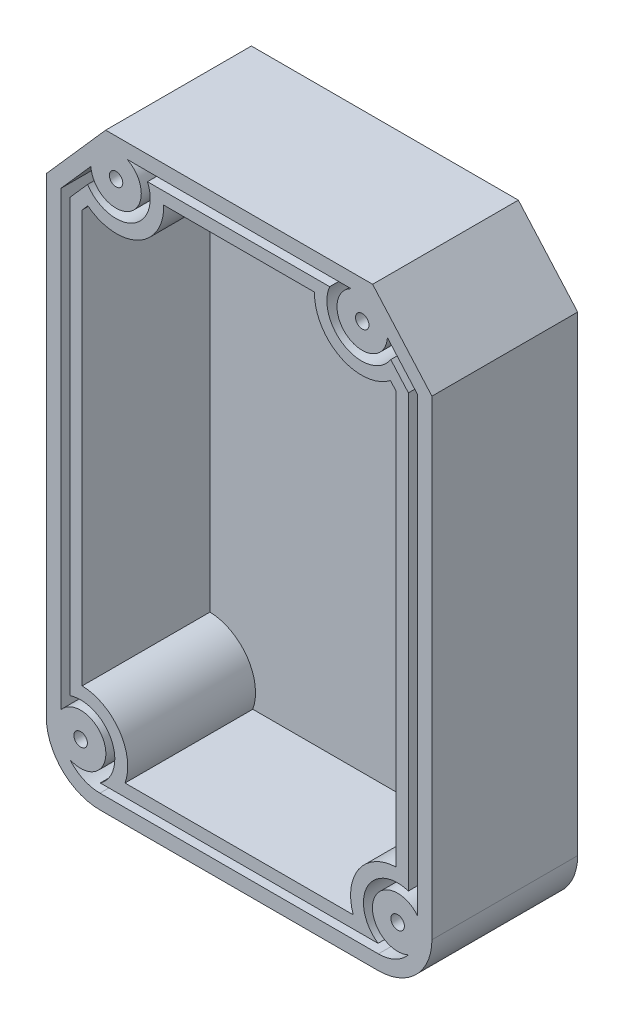
SolidWorks part; units mm, degrees
ref_plane "Front Plane" through (0, 0, 0) normal (0, 0, 1) x (1, 0, 0)
ref_plane "Top Plane" through (0, 0, 0) normal (0, 1, 0) x (1, 0, 0)
ref_plane "Right Plane" through (0, 0, 0) normal (1, 0, 0) x (0, 0, -1)
sketch "Sketch1" plane through (0, 0, 0) normal (0, 0, 1) x (1, 0, 0)
  line L3 (-1355.6942, -734.7459) -> (-1355.6942, -839.7459)
  line L4 (-1367.6432, -851.6949) -> (-1429.7452, -851.6949)
  line L5 (-1441.6942, -839.7459) -> (-1441.6942, -734.7459)
  line L6 (-1441.6942, -734.7459) -> (-1428.4655, -719.7459)
  line L7 (-1428.4655, -719.7459) -> (-1368.923, -719.7459)
  line L8 (-1368.923, -719.7459) -> (-1355.6942, -734.7459)
  arc A0 (-1355.6942, -839.7459) -> (-1367.6432, -851.6949) centre (-1367.6432, -839.7459) cw
  arc A1 (-1429.7452, -851.6949) -> (-1441.6942, -839.7459) centre (-1429.7452, -839.7459) cw
  dimension "D5" = 11.949
  dimension "D6" = 11.949
  dimension "D1" = 105
  dimension "D2" = 86
  dimension "D3" = 15
  dimension "D4" = 20
extrude "Boss-Extrude1" add sketch "Sketch1" along normal blind 32.5 contours L3 A0 L4 A1 L5 L6 L7 L8
sketch "Sketch2" plane through (0, 0, 32.5) normal (0, 0, 1) x (1, 0, 0)
  line L6 (-1355.6942, -734.7459) -> (-1368.923, -719.7459)
  line L7 (-1368.923, -719.7459) -> (-1428.4655, -719.7459)
  line L8 (-1428.4655, -719.7459) -> (-1441.6942, -734.7459)
  line L9 (-1441.6942, -734.7459) -> (-1441.6942, -839.7459)
  line L10 (-1429.7452, -851.6949) -> (-1367.6432, -851.6949)
  line L11 (-1355.6942, -839.7459) -> (-1355.6942, -734.7459)
  line L12 (-1355.6942, -734.7459) -> (-1368.923, -719.7459)
  line L13 (-1368.923, -719.7459) -> (-1428.4655, -719.7459)
  line L14 (-1428.4655, -719.7459) -> (-1441.6942, -734.7459)
  line L15 (-1441.6942, -734.7459) -> (-1441.6942, -839.7459)
  line L16 (-1429.7452, -851.6949) -> (-1367.6432, -851.6949)
  line L17 (-1355.6942, -839.7459) -> (-1355.6942, -734.7459)
  line L18 (-1358.9442, -735.9743) -> (-1370.3901, -722.9959)
  line L19 (-1370.3901, -722.9959) -> (-1426.9984, -722.9959)
  line L20 (-1426.9984, -722.9959) -> (-1438.4442, -735.9743)
  line L21 (-1438.4442, -735.9743) -> (-1438.4442, -839.7459)
  line L22 (-1429.7452, -848.4449) -> (-1367.6432, -848.4449)
  line L23 (-1358.9442, -839.7459) -> (-1358.9442, -735.9743)
  arc A2 (-1441.6942, -839.7459) -> (-1429.7452, -851.6949) centre (-1429.7452, -839.7459) ccw
  arc A3 (-1367.6432, -851.6949) -> (-1355.6942, -839.7459) centre (-1367.6432, -839.7459) ccw
  arc A4 (-1441.6942, -839.7459) -> (-1429.7452, -851.6949) centre (-1429.7452, -839.7459) ccw
  arc A5 (-1367.6432, -851.6949) -> (-1355.6942, -839.7459) centre (-1367.6432, -839.7459) ccw
  arc A6 (-1438.4442, -839.7459) -> (-1429.7452, -848.4449) centre (-1429.7452, -839.7459) ccw
  arc A7 (-1367.6432, -848.4449) -> (-1358.9442, -839.7459) centre (-1367.6432, -839.7459) ccw
  dimension "D1" = 0
  dimension "D2" = 3.25
extrude "Cut-Extrude3" cut sketch "Sketch2" along direction (0, 0, -1) on the side against the normal offset from surface 4 and the other way through all contours L18 L19 L20 L21 A6 L22 A7 L23
sketch "Sketch32" plane through (0, 0, 4) normal (0, 0, 1) x (1, 0, 0)
  line L2 (-1398.6942, -848.4449) -> (-1398.6942, -844.105) construction
  line L3 (-1429.7452, -848.4449) -> (-1367.6432, -848.4449) construction
  line L10 (-1358.9442, -839.7459) -> (-1358.9442, -735.9743)
  line L11 (-1358.9442, -735.9743) -> (-1370.3901, -722.9959)
  line L12 (-1370.3901, -722.9959) -> (-1426.9984, -722.9959)
  line L13 (-1426.9984, -722.9959) -> (-1438.4442, -735.9743)
  line L14 (-1438.4442, -735.9743) -> (-1438.4442, -839.7459)
  line L15 (-1429.7452, -848.4449) -> (-1367.6432, -848.4449)
  line L21 (-1398.6942, -848.4449) -> (-1367.6432, -848.4449)
  circle A8 centre (-1426.1484, -728.0459) radius 1.5
  circle A9 centre (-1426.1484, -728.0459) radius 5.625
  arc A10 (-1438.4442, -839.7459) -> (-1429.7452, -848.4449) centre (-1429.7452, -839.7459) ccw
  arc A11 (-1367.6432, -848.4449) -> (-1358.9442, -839.7459) centre (-1367.6432, -839.7459) ccw
  circle A14 centre (-1371.2401, -728.0459) radius 1.5
  circle A15 centre (-1371.2401, -728.0459) radius 5.625
  circle A16 centre (-1434.0452, -840.1949) radius 1.5
  circle A17 centre (-1434.0452, -840.1949) radius 5.625
  circle A18 centre (-1363.3432, -840.1949) radius 1.5
  circle A19 centre (-1363.3432, -840.1949) radius 5.625
  dimension "D2" = 3
  dimension "D5" = 0.85
  dimension "D6" = 0.85
  dimension "D9" = 4.3
  dimension "D10" = 11.25
  dimension "D3" = 11.25
  dimension "D4" = 5.05
  dimension "D7" = 8.25
  dimension "D8" = 4.3
  dimension "D11" = 0
extrude "Boss-Extrude5" add sketch "Sketch32" along direction (0, 0, -1) on the side of the normal up to surface (28.5 mm away) contours A9 | A15 | A17 | A19 | A8 | A14 | A18 | A16
sketch "Sketch33" plane through (0, 0, 4) normal (0, 0, 1) x (1, 0, 0)
  circle A8 centre (-1363.3432, -840.1949) radius 1.5 construction
  circle A9 centre (-1434.0452, -840.1949) radius 1.5 construction
  circle A10 centre (-1426.1484, -728.0459) radius 1.5 construction
  circle A11 centre (-1371.2401, -728.0459) radius 1.5 construction
  circle A12 centre (-1363.3432, -840.1949) radius 1.5
  circle A13 centre (-1434.0452, -840.1949) radius 1.5
  circle A14 centre (-1426.1484, -728.0459) radius 1.5
  circle A15 centre (-1371.2401, -728.0459) radius 1.5
  dimension "D1" = 3
extrude "Cut-Extrude15" cut sketch "Sketch33" along direction (0, 0, -1) on the side against the normal up to surface (4 mm away)
sketch "Sketch34" plane through (0, 0, 4) normal (0, 0, 1) x (1, 0, 0)
  line L31 (-1429.4626, -846.4449) -> (-1367.9258, -846.4449)
  line L32 (-1436.4442, -736.7302) -> (-1436.4442, -832.9571)
  line L33 (-1432.5096, -732.2688) -> (-1436.4442, -736.7302)
  line L34 (-1378.5018, -724.9959) -> (-1418.8866, -724.9959)
  line L35 (-1360.9442, -736.7302) -> (-1364.8788, -732.2688)
  line L36 (-1360.9442, -832.9571) -> (-1360.9442, -736.7302)
  line L37 (-1363.6942, -829.7008) -> (-1363.6942, -737.7696)
  line L38 (-1363.6942, -737.7696) -> (-1364.9483, -736.3476)
  line L39 (-1381.8729, -727.7459) -> (-1415.5155, -727.7459)
  line L40 (-1432.4402, -736.3476) -> (-1433.6942, -737.7696)
  line L41 (-1433.6942, -737.7696) -> (-1433.6942, -829.7008)
  line L43 (-1424.1457, -843.6949) -> (-1373.2427, -843.6949)
  line L45 (-1367.6432, -848.4449) -> (-1429.7452, -848.4449) construction
  line L46 (-1438.4442, -836.6893) -> (-1438.4442, -735.9743) construction
  line L47 (-1367.6432, -848.4449) -> (-1429.7452, -848.4449)
  line L48 (-1438.4442, -836.6893) -> (-1438.4442, -735.9743)
  line L49 (-1438.4442, -735.9743) -> (-1431.7623, -728.3978) construction
  line L50 (-1438.4442, -735.9743) -> (-1431.7623, -728.3978)
  line L51 (-1355.6942, -734.7459) -> (-1368.923, -719.7459)
  line L52 (-1368.923, -719.7459) -> (-1428.4655, -719.7459)
  line L53 (-1428.4655, -719.7459) -> (-1441.6942, -734.7459)
  line L54 (-1441.6942, -734.7459) -> (-1441.6942, -839.7459)
  line L55 (-1429.7452, -851.6949) -> (-1367.6432, -851.6949)
  line L56 (-1355.6942, -839.7459) -> (-1355.6942, -734.7459)
  line L57 (-1355.6942, -734.7459) -> (-1368.923, -719.7459)
  line L58 (-1368.923, -719.7459) -> (-1428.4655, -719.7459)
  line L59 (-1428.4655, -719.7459) -> (-1441.6942, -734.7459)
  line L60 (-1441.6942, -734.7459) -> (-1441.6942, -839.7459)
  line L61 (-1429.7452, -851.6949) -> (-1367.6432, -851.6949)
  line L62 (-1355.6942, -839.7459) -> (-1355.6942, -734.7459)
  line L63 (-1358.9442, -735.9743) -> (-1365.6261, -728.3978) construction
  line L64 (-1358.9442, -735.9743) -> (-1365.6261, -728.3978)
  line L65 (-1358.9442, -735.9743) -> (-1358.9442, -836.6893) construction
  line L66 (-1358.9442, -735.9743) -> (-1358.9442, -836.6893)
  line L68 (-1360.9442, -736.7302) -> (-1360.9442, -832.9571)
  line L69 (-1360.9442, -735.9743) -> (-1360.9442, -832.9571) construction
  line L70 (-1360.9442, -832.8256) -> (-1360.9442, -736.7302) construction
  line L71 (-1367.7111, -846.4449) -> (-1429.6774, -846.4449)
  line L72 (-1436.4442, -832.9571) -> (-1436.4442, -736.7302)
  line L73 (-1436.4442, -736.7302) -> (-1432.5025, -732.2608)
  line L74 (-1419.1388, -725.0449) -> (-1378.5018, -724.9959)
  line L75 (-1436.4442, -736.7302) -> (-1436.4442, -832.8256) construction
  arc A48 (-1378.5018, -724.9959) -> (-1364.8788, -732.2688) centre (-1371.3772, -728.0459) ccw
  arc A49 (-1363.6942, -829.7008) -> (-1373.2427, -843.6949) centre (-1363.3432, -840.1949) ccw
  arc A50 (-1381.8729, -727.7459) -> (-1364.9483, -736.3476) centre (-1371.3772, -728.0459) ccw
  arc A51 (-1432.4402, -736.3476) -> (-1415.5155, -727.7459) centre (-1426.0112, -728.0459) ccw
  arc A52 (-1358.9442, -836.6893) -> (-1360.9271, -845.2746) centre (-1363.3432, -840.1949) ccw construction
  arc A53 (-1424.1457, -843.6949) -> (-1433.6942, -829.7008) centre (-1434.0452, -840.1949) ccw
  arc A54 (-1427.8366, -848.6627) -> (-1433.6942, -829.7008) centre (-1434.0452, -840.1949) ccw construction
  arc A55 (-1363.6942, -829.7008) -> (-1369.5519, -848.6627) centre (-1363.3432, -840.1949) ccw construction
  arc A60 (-1358.9442, -836.6893) -> (-1360.9271, -845.2746) centre (-1363.3432, -840.1949) ccw
  arc A61 (-1436.4614, -845.2746) -> (-1438.4442, -836.6893) centre (-1434.0452, -840.1949) ccw construction
  arc A62 (-1436.4614, -845.2746) -> (-1438.4442, -836.6893) centre (-1434.0452, -840.1949) ccw
  arc A63 (-1441.6942, -839.7459) -> (-1429.7452, -851.6949) centre (-1429.7452, -839.7459) ccw
  arc A64 (-1367.6432, -851.6949) -> (-1355.6942, -839.7459) centre (-1367.6432, -839.7459) ccw
  arc A65 (-1441.6942, -839.7459) -> (-1429.7452, -851.6949) centre (-1429.7452, -839.7459) ccw
  arc A66 (-1367.6432, -851.6949) -> (-1355.6942, -839.7459) centre (-1367.6432, -839.7459) ccw
  arc A67 (-1436.4614, -845.2746) -> (-1429.7452, -848.4449) centre (-1429.7452, -839.7459) ccw construction
  arc A68 (-1436.4614, -845.2746) -> (-1429.7452, -848.4449) centre (-1429.7452, -839.7459) ccw
  arc A69 (-1367.6432, -848.4449) -> (-1360.9271, -845.2746) centre (-1367.6432, -839.7459) ccw construction
  arc A70 (-1367.6432, -848.4449) -> (-1360.9271, -845.2746) centre (-1367.6432, -839.7459) ccw
  arc A71 (-1431.7623, -728.3978) -> (-1423.6708, -722.9959) centre (-1426.1484, -728.0459) ccw construction
  arc A72 (-1431.7623, -728.3978) -> (-1423.6708, -722.9959) centre (-1426.1484, -728.0459) ccw
  arc A73 (-1373.7176, -722.9959) -> (-1365.6261, -728.3978) centre (-1371.2401, -728.0459) ccw construction
  arc A74 (-1373.7176, -722.9959) -> (-1365.6261, -728.3978) centre (-1371.2401, -728.0459) ccw
  arc A75 (-1360.9442, -832.9571) -> (-1367.7111, -846.4449) centre (-1363.3432, -840.1949) ccw
  arc A76 (-1367.7111, -846.4449) -> (-1367.7111, -846.4449) centre (-1367.7111, -846.4449) cw
  arc A77 (-1429.6774, -846.4449) -> (-1429.6774, -846.4449) centre (-1429.6774, -846.4449) cw
  arc A78 (-1429.6774, -846.4449) -> (-1436.4442, -832.9571) centre (-1434.0452, -840.1949) ccw
  arc A79 (-1432.5025, -732.2608) -> (-1419.1388, -725.0449) centre (-1426.1484, -728.0459) ccw
  arc A80 (-1432.5096, -732.2688) -> (-1418.8866, -724.9959) centre (-1426.0112, -728.0459) ccw construction
  arc A81 (-1432.5025, -732.2608) -> (-1422.7899, -721.2004) centre (-1426.1484, -728.0459) ccw construction
  arc A82 (-1360.9442, -832.8256) -> (-1367.9258, -846.4449) centre (-1363.3432, -840.1949) ccw construction
  arc A83 (-1429.4626, -846.4449) -> (-1436.4442, -832.8256) centre (-1434.0452, -840.1949) ccw construction
  point P32 (-1421.2539, -737.4064)
  point P33 (-1423.0252, -732.7242)
  dimension "D1" = 0
  dimension "D3" = 2
  dimension "D2" = 5.006
  dimension "D4" = 2.75
extrude "Boss-Extrude6" add sketch "Sketch34" along normal up to surface (28.5 mm away) separate body contours A79 L73 L33 L32 A78 L71 L31 A75 L36 L35 A48 L74 L43 A53 L41 L40 A51 L39 A50 L38 L37 A49 up to face at (-1398.6942, -787.2507, 32.5)
